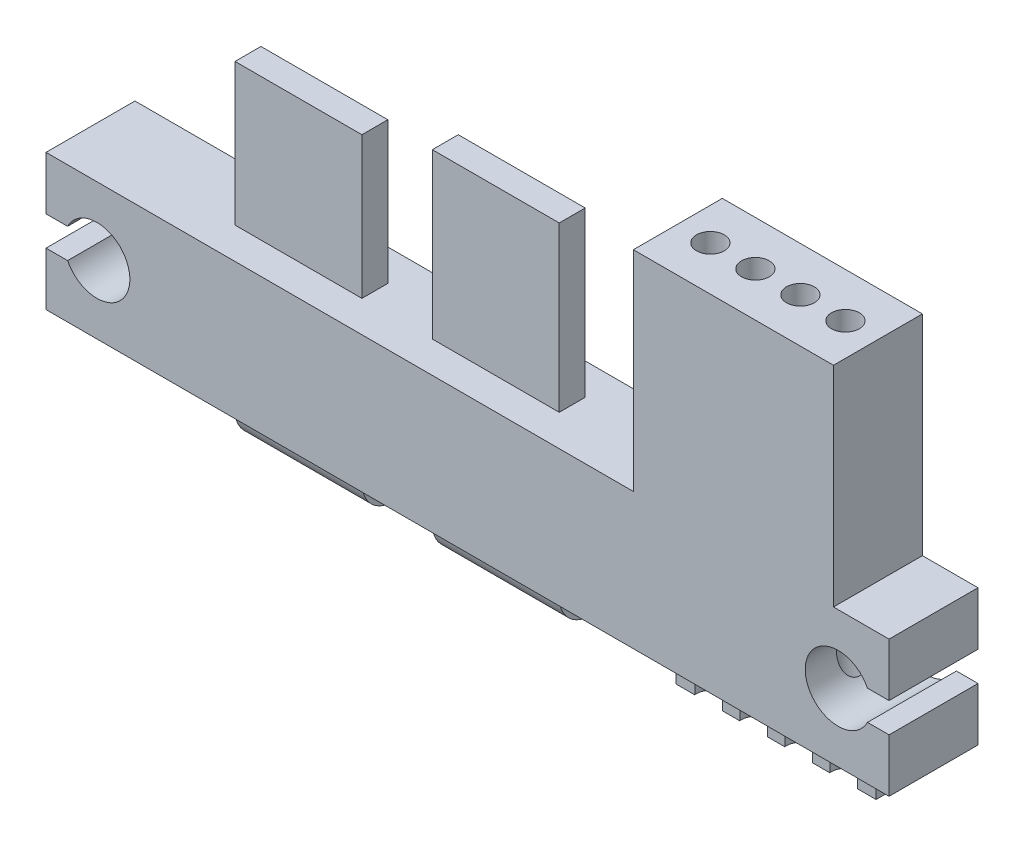
SolidWorks part; units mm, degrees
material "黄铜"
ref_plane "前视基准面" through (0, 0, 0) normal (0, 0, 1) x (1, 0, 0)
ref_plane "上视基准面" through (0, 0, 0) normal (0, 1, 0) x (1, 0, 0)
ref_plane "右视基准面" through (0, 0, 0) normal (1, 0, 0) x (0, 0, -1)
sketch "草图1" plane through (0, 0, 0) normal (0, 0, 1) x (1, 0, 0)
  line L0 (0, 13.4013) -> (0, -14.5066) construction
  line L1 (-22.75, 7.35) -> (-22.75, 0)
  line L2 (22.75, 7.35) -> (22.75, 0)
  line L3 (-22.75, 7.35) -> (8.95, 7.35)
  line L4 (8.95, 7.35) -> (8.95, 18.65)
  line L5 (8.95, 18.65) -> (19.75, 18.65)
  line L6 (19.75, 18.65) -> (19.75, 7.35)
  line L7 (19.75, 7.35) -> (22.75, 7.35)
  line L8 (-22.75, 0) -> (22.75, 0)
  dimension "D1" = 45.5
  dimension "D2" = 7.35
  dimension "D3" = 10.8
  dimension "D4" = 3
  dimension "D5" = 11.3
extrude "凸台-拉伸1" add sketch "草图1" along normal mid plane 4.8
sketch "草图2" plane through (0, 7.35, 0) normal (0, 1, 0) x (1, 0, 0)
  line L0 (-5.5, 8.3691) -> (-5.5, -6.6933) construction
  line L1 (-14.25, 0.7) -> (-7.4, 0.7)
  line L2 (-14.25, 0.7) -> (-14.25, -0.7)
  line L3 (-14.25, -0.7) -> (-7.4, -0.7)
  line L4 (-7.4, 0.7) -> (-7.4, -0.7)
  line L5 (-3.6, 0.7) -> (-3.6, -0.7)
  line L6 (3.25, -0.7) -> (-3.6, -0.7)
  line L7 (3.25, 0.7) -> (3.25, -0.7)
  line L8 (3.25, 0.7) -> (-3.6, 0.7)
  line L9 (-22.75, -2.4) -> (-22.75, 2.4) construction
  point P8 (-14.25, 0)
  dimension "D1" = 1.4
  dimension "D2" = 6.85
  dimension "D3" = 3.8
  dimension "D4" = 8.5
extrude "凸台-拉伸2" add sketch "草图2" along normal blind 7.65
sketch "草图3" plane through (0, 15, 0) normal (0, 1, 0) x (1, 0, 0)
  line L4 (3.25, 0.7) -> (-3.6, 0.7)
  line L5 (-3.6, 0.7) -> (-3.6, -0.7)
  line L6 (-3.6, -0.7) -> (3.25, -0.7)
  line L7 (3.25, -0.7) -> (3.25, 0.7)
  line L8 (3.25, 0.7) -> (-3.6, 0.7)
  line L9 (-3.6, 0.7) -> (-3.6, -0.7)
  line L10 (-3.6, -0.7) -> (3.25, -0.7)
  line L11 (3.25, -0.7) -> (3.25, 0.7)
  dimension "D1" = 0
extrude "凸台-拉伸3" add sketch "草图3" along normal blind 1.2
sketch "草图4" plane through (0, 0, 0) normal (1, 0, 0) x (0, 0, -1)
  line L0 (0, 0) -> (0, -1.3)
  line L1 (1, -2.3) -> (5, -2.3)
  arc A0 (1, -2.3) -> (0, -1.3) centre (1, -1.3) cw
  point P6 (0, -2.3)
  dimension "D3" = 1
  dimension "D1" = 2.3
  dimension "D2" = 5
sketch "草图5" plane through (0, 0, 0) normal (0, -1, 0) x (1, 0, 0)
  line L0 (3.25, 0.7) -> (3.25, -0.7) construction
  line L1 (3.25, -0.7) -> (-3.6, -0.7) construction
  line L2 (-3.6, -0.7) -> (-3.6, 0.7) construction
  line L3 (-3.6, 0.7) -> (3.25, 0.7) construction
  line L4 (-14.25, -0.7) -> (-14.25, 0.7) construction
  line L5 (-14.25, 0.7) -> (-7.4, 0.7) construction
  line L6 (-7.4, 0.7) -> (-7.4, -0.7) construction
  line L7 (-7.4, -0.7) -> (-14.25, -0.7) construction
  line L8 (3.25, 0.7) -> (3.25, -0.7)
  line L9 (3.25, -0.7) -> (-3.6, -0.7)
  line L10 (-3.6, -0.7) -> (-3.6, 0.7)
  line L11 (-3.6, 0.7) -> (3.25, 0.7)
  line L12 (-14.25, -0.7) -> (-14.25, 0.7)
  line L13 (-14.25, 0.7) -> (-7.4, 0.7)
  line L14 (-7.4, 0.7) -> (-7.4, -0.7)
  line L15 (-7.4, -0.7) -> (-14.25, -0.7)
sweep "扫描1" add profiles "草图5" path "草图4"
sketch "草图6" plane through (0, 0, 0) normal (0, -1, 0) x (1, 0, 0)
  line L0 (17.35, 0.1) -> (16.15, 0.1)
  line L1 (19.75, 0.1) -> (18.55, 0.1)
  line L2 (19.75, 0.1) -> (19.75, -2.4)
  line L3 (19.75, -2.4) -> (18.55, -2.4)
  line L4 (18.55, 0.1) -> (18.55, -2.4)
  line L5 (17.35, 0.1) -> (17.35, -2.4)
  line L6 (17.35, -2.4) -> (16.15, -2.4)
  line L7 (16.15, 0.1) -> (16.15, -2.4)
  line L8 (14.95, 0.1) -> (13.75, 0.1)
  line L9 (14.95, 0.1) -> (14.95, -2.4)
  line L10 (14.95, -2.4) -> (13.75, -2.4)
  line L11 (13.75, 0.1) -> (13.75, -2.4)
  line L12 (12.55, 0.1) -> (11.35, 0.1)
  line L13 (12.55, 0.1) -> (12.55, -2.4)
  line L14 (12.55, -2.4) -> (11.35, -2.4)
  line L15 (11.35, 0.1) -> (11.35, -2.4)
  line L16 (10.15, 0.1) -> (8.95, 0.1)
  line L17 (10.15, 0.1) -> (10.15, -2.4)
  line L18 (10.15, -2.4) -> (8.95, -2.4)
  line L19 (8.95, 0.1) -> (8.95, -2.4)
  line L20 (-22.75, -2.4) -> (22.75, -2.4) construction
  dimension "D1" = 1.2
  dimension "D2" = 2.5
  dimension "D3" = 5
extrude "凸台-拉伸4" add sketch "草图6" along normal blind 2.8
sketch "草图7" plane through (0, 0, 2.4) normal (0, 0, 1) x (1, 0, 0)
  line L0 (0, 23.7268) -> (0, -9.9476) construction
  line L1 (-21.5845, 4.475) -> (-22.75, 4.475)
  line L2 (-22.75, 7.35) -> (-22.75, 0) construction
  line L3 (-21.5845, 2.875) -> (-22.75, 2.875)
  line L4 (-22.75, 2.875) -> (-22.75, 4.475)
  line L5 (22.75, 0) -> (22.75, 7.35) construction
  line L6 (22.75, 2.875) -> (22.75, 4.475)
  line L7 (21.5845, 2.875) -> (22.75, 2.875)
  line L8 (21.5845, 4.475) -> (22.75, 4.475)
  arc A0 (-21.5845, 2.875) -> (-21.5845, 4.475) centre (-20, 3.675) ccw
  arc A1 (21.5845, 2.875) -> (21.5845, 4.475) centre (20, 3.675) cw
  point P12 (22.75, 3.675)
  dimension "D2" = 1.775
  dimension "D3" = 40
  dimension "D1" = 1.6
extrude "切除-拉伸1" cut sketch "草图7" against normal through all
sketch "草图8" plane through (0, 18.65, 0) normal (0, 1, 0) x (1, 0, 0)
  line L0 (14.35, 4.6676) -> (14.35, -5.9072) construction
  line L1 (19.75, 2.4) -> (8.95, 2.4) construction
  line L2 (8.95, -2.4) -> (8.95, 2.4) construction
  circle A0 centre (10.7066, 0) radius 0.75
  circle A1 centre (13.1355, 0) radius 0.75
  circle A2 centre (15.5645, 0) radius 0.75
  circle A3 centre (17.9934, 0) radius 0.75
  point P4 (14.35, 2.4)
  point P12 (8.95, 0)
  dimension "D1" = 1.5
  dimension "D2" = 4
extrude "切除-拉伸2" cut sketch "草图8" against normal through all
